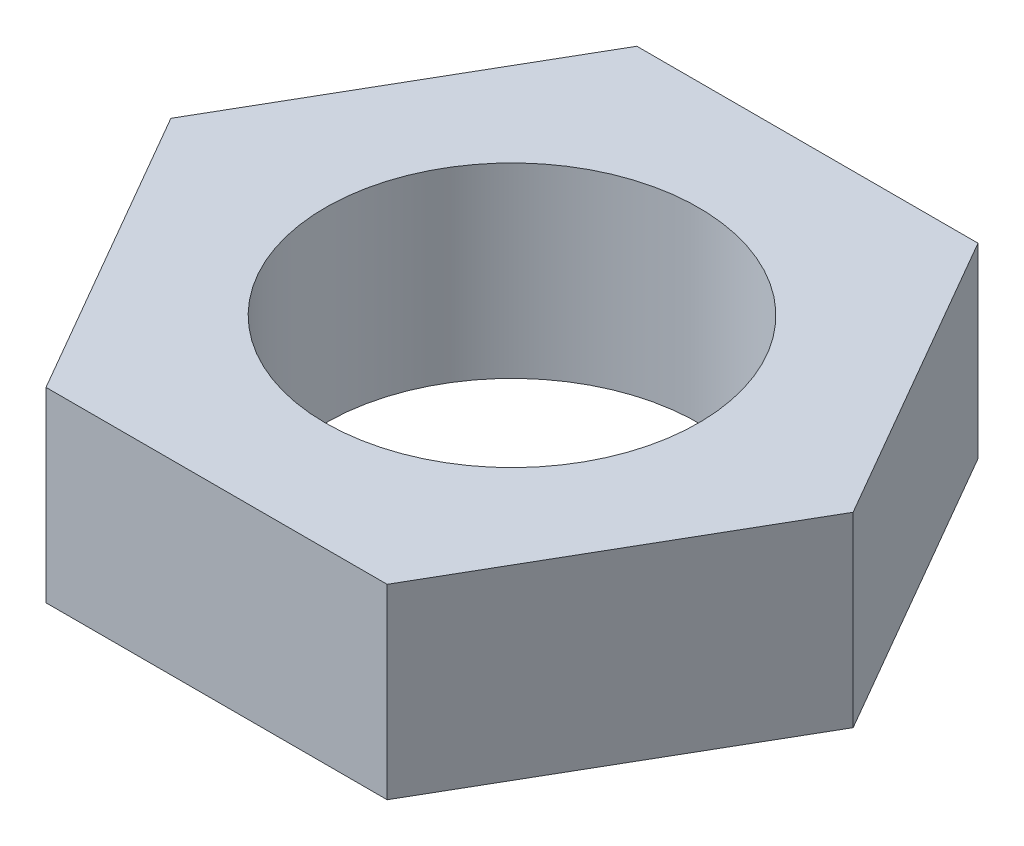
SolidWorks part; units mm, degrees
material "AISI Type A2 Tool Steel"
ref_plane "Front Plane" through (0, 0, 0) normal (0, 0, 1) x (1, 0, 0)
ref_plane "Top Plane" through (0, 0, 0) normal (0, 1, 0) x (1, 0, 0)
ref_plane "Right Plane" through (0, 0, 0) normal (1, 0, 0) x (0, 0, -1)
sketch "Sketch1" plane through (0, 0, 0) normal (0, 1, 0) x (1, 0, 0)
  line L1 (10.9697, 0) -> (5.4848, 9.5)
  line L2 (5.4848, 9.5) -> (-5.4848, 9.5)
  line L3 (-5.4848, 9.5) -> (-10.9697, 0)
  line L4 (-10.9697, 0) -> (-5.4848, -9.5)
  line L5 (-5.4848, -9.5) -> (5.4848, -9.5)
  line L6 (5.4848, -9.5) -> (10.9697, 0)
  circle A0 centre (0, 0) radius 9.5 construction
  dimension "D1" = 19
extrude "Boss-Extrude1" add sketch "Sketch1" against normal blind 6
sketch "Sketch2" plane through (0, 0, 0) normal (0, 1, 0) x (1, 0, 0)
  circle A0 centre (0, 0) radius 6
  dimension "D1" = 12
extrude "Cut-Extrude1" cut sketch "Sketch2" against normal blind 6
